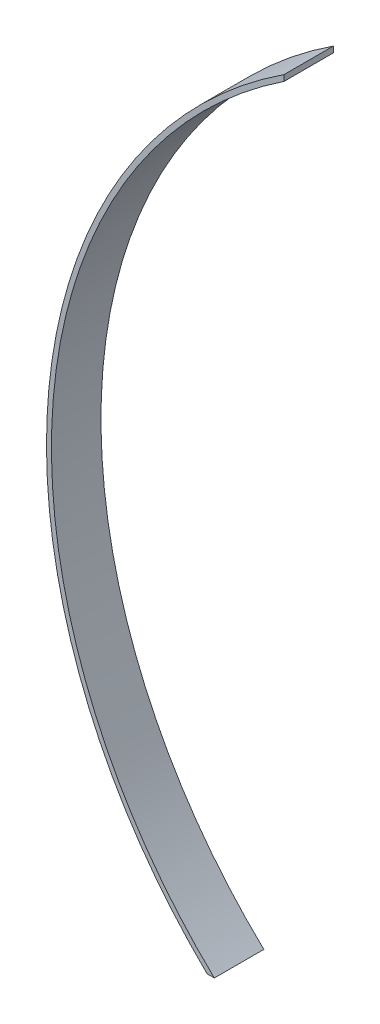
SolidWorks part; units mm, degrees
ref_plane "Front Plane" through (0, 0, 0) normal (0, 0, 1) x (1, 0, 0)
ref_plane "Top Plane" through (0, 0, 0) normal (0, 1, 0) x (1, 0, 0)
ref_plane "Right Plane" through (0, 0, 0) normal (1, 0, 0) x (0, 0, -1)
sketch "Sketch1" plane through (0, 0, 0) normal (0, 0, 1) x (1, 0, 0)
  line L0 (-53.2508, 21.1713) -> (18.1027, 21.1713) construction
  line L1 (-10.9373, 21.1713) -> (-10.9373, 203.005) construction
  line L2 (-10.9373, 185) -> (-10.9373, 186.1975)
  line L11 (-25, 21.1713) -> (-26.4486, 21.1713)
  arc A0 (-10.9373, 185) -> (-25, 21.1713) centre (47.1036, 97.5) ccw
  arc A2 (-10.9373, 186.1975) -> (-26.4486, 21.1713) centre (47.1036, 97.5) ccw
  dimension "D8" = 105
  dimension "D1" = 106
extrude "Boss-Extrude1" add sketch "Sketch1" along normal blind 10
